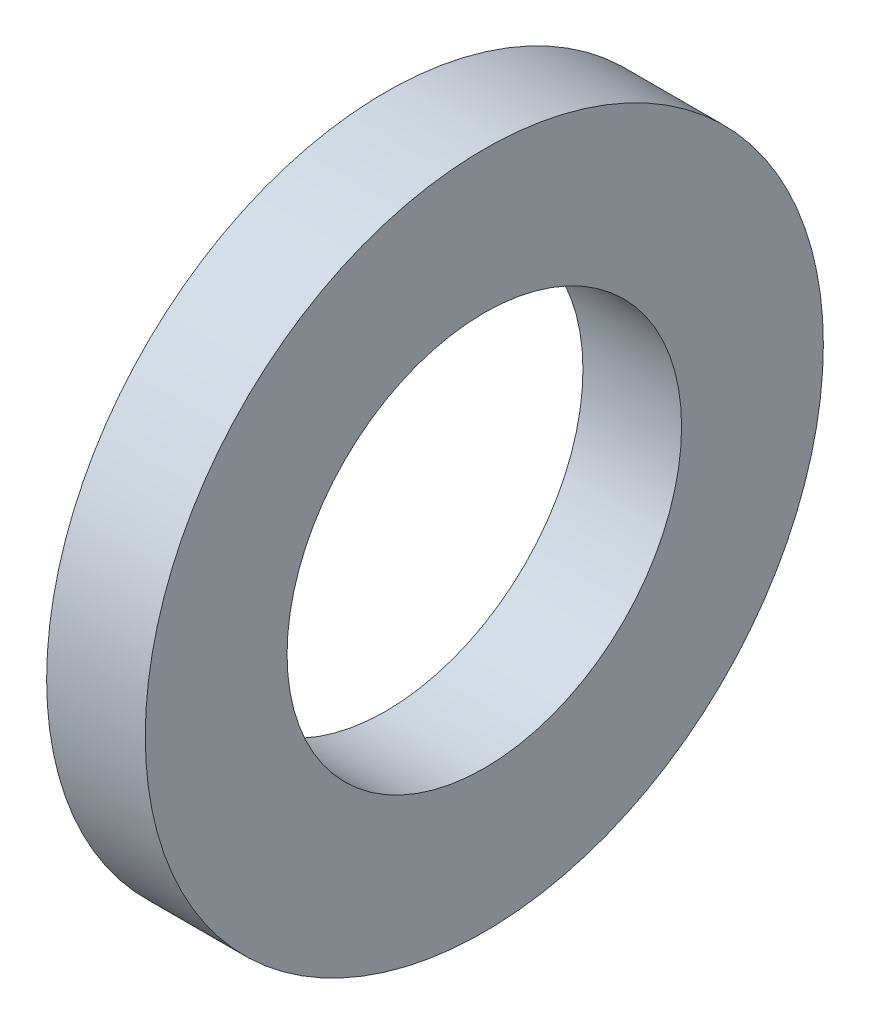
SolidWorks part; units mm, degrees
ref_plane "Plane1" through (0, 0, 0) normal (0, 0, 1) x (1, 0, 0)
ref_plane "Plane2" through (0, 0, 0) normal (0, 1, 0) x (1, 0, 0)
ref_plane "Plane3" through (0, 0, 0) normal (1, 0, 0) x (0, 0, -1)
sketch "Sketch1" plane through (0, 0, 0) normal (0, 0, 1) x (1, 0, 0)
  line L0 (-34.925, 0) -> (9.525, 0) construction
  line L1 (0, 3.2) -> (0, 5.5)
  line L2 (0, 5.5) -> (-1.6, 5.5)
  line L3 (-1.6, 5.5) -> (-1.6, 3.2)
  line L4 (-1.6, 3.2) -> (0, 3.2)
  dimension "Thickness" = 1.6
  dimension "Inside_dia" = 6.4
  dimension "Outside_dia" = 11
revolve "Base-Revolve" add sketch "Sketch1" angle 360 about L0
